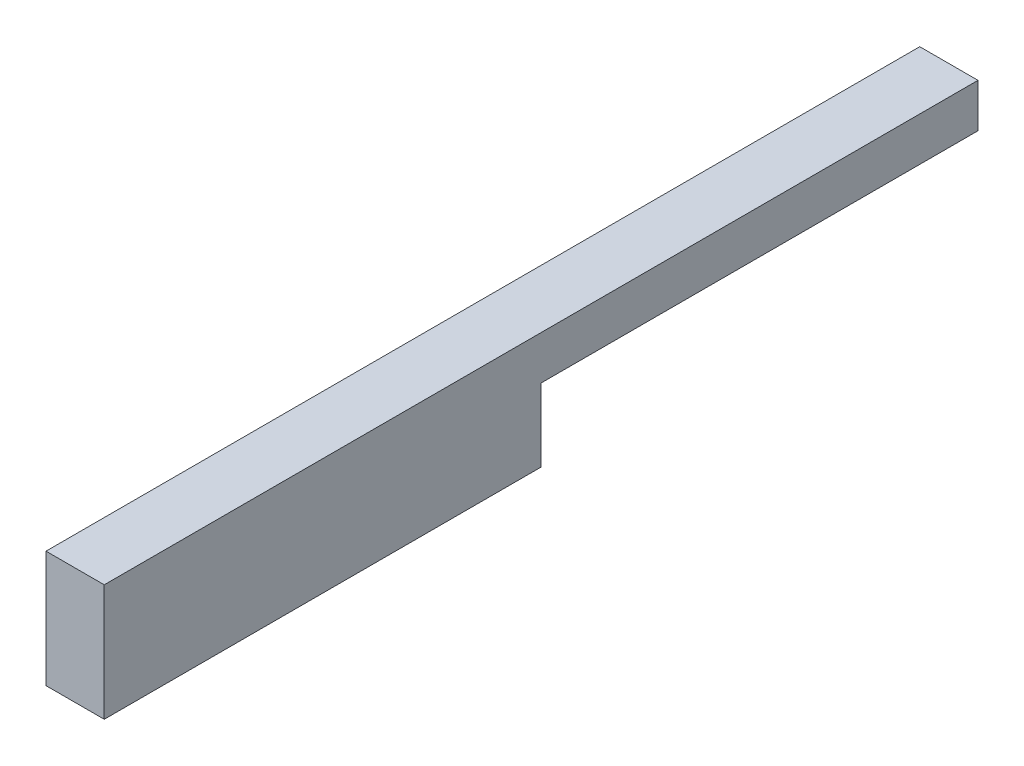
SolidWorks part; units mm, degrees
ref_plane "Front Plane" through (0, 0, 0) normal (0, 0, 1) x (1, 0, 0)
ref_plane "Top Plane" through (0, 0, 0) normal (0, 1, 0) x (1, 0, 0)
ref_plane "Right Plane" through (0, 0, 0) normal (1, 0, 0) x (0, 0, -1)
sketch "Sketch1" plane through (0, 0, 0) normal (1, 0, 0) x (0, 0, -1)
  line L0 (-19.987, 0.9993) -> (-19.987, -0.3838)
  line L1 (40.013, -2.0007) -> (10.013, -2.0007)
  line L2 (40.013, -2.0007) -> (40.013, 0.9993)
  line L3 (40.013, 0.9993) -> (-19.987, 0.9993)
  line L5 (40.013, -2.0007) -> (-19.987, 0.9993) construction
  line L6 (40.013, 0.9993) -> (0, 0) construction
  line L7 (-19.987, -0.3838) -> (-19.987, -7.0007)
  line L8 (-19.987, -7.0007) -> (10.013, -7.0007)
  line L9 (10.013, -7.0007) -> (10.013, -2.0007)
  point P0 (0, 0)
  point P10 (0, 0)
  point P11 (0, 0)
  point P12 (0, 0)
  point P13 (0, 0)
  dimension "D1" = 60
  dimension "D2" = 30
  dimension "D3" = 8
  dimension "D4" = 3
extrude "Boss-Extrude1" add sketch "Sketch1" along normal blind 4
